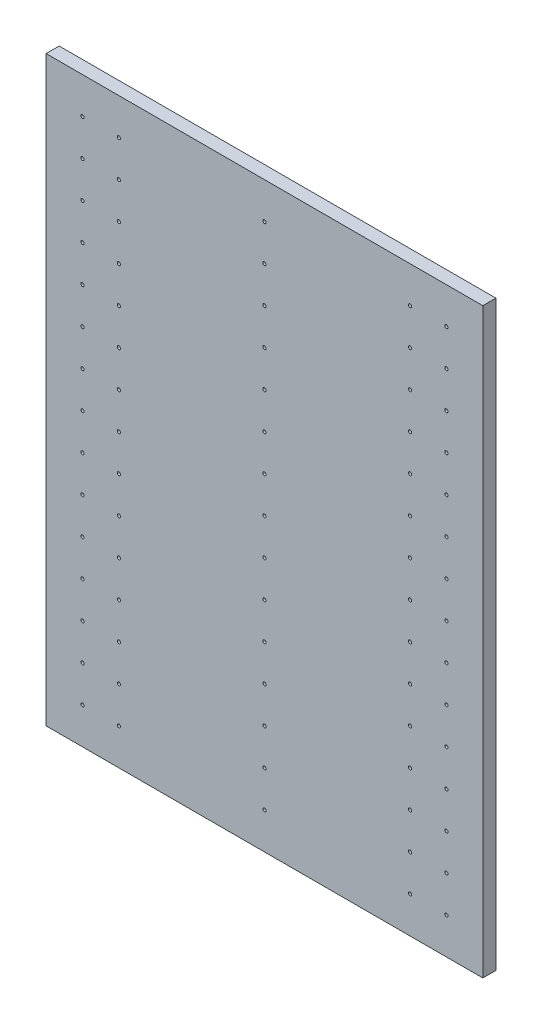
SolidWorks part; units mm, degrees
ref_plane "Спереди" through (0, 0, 0) normal (0, 0, 1) x (1, 0, 0)
ref_plane "Сверху" through (0, 0, 0) normal (0, 1, 0) x (1, 0, 0)
ref_plane "Справа" through (0, 0, 0) normal (1, 0, 0) x (0, 0, -1)
sketch "Эскиз1" plane through (0, 0, 0) normal (0, 0, 1) x (1, 0, 0)
  line L1 (0, 0) -> (600, 0)
  line L2 (0, 0) -> (0, 800)
  line L3 (0, 800) -> (600, 800)
  line L4 (600, 0) -> (600, 800)
extrude "Бобышка-Вытянуть1" add sketch "Эскиз1" along normal blind 18
sketch "Эскиз2" plane through (0, 0, 18) normal (0, 0, 1) x (1, 0, 0)
  circle A0 centre (550, 50) radius 2.25
  circle A1 centre (300, 50) radius 2.25
  circle A2 centre (500, 50) radius 2.25
  circle A3 centre (100, 50) radius 2.25
  circle A4 centre (50, 50) radius 2.25
  circle A60 centre (550, 100) radius 2.25
  circle A61 centre (300, 100) radius 2.25
  circle A62 centre (500, 100) radius 2.25
  circle A63 centre (100, 100) radius 2.25
  circle A64 centre (50, 100) radius 2.25
  circle A65 centre (550, 150) radius 2.25
  circle A66 centre (300, 150) radius 2.25
  circle A67 centre (500, 150) radius 2.25
  circle A68 centre (100, 150) radius 2.25
  circle A69 centre (50, 150) radius 2.25
  circle A70 centre (550, 200) radius 2.25
  circle A71 centre (300, 200) radius 2.25
  circle A72 centre (500, 200) radius 2.25
  circle A73 centre (100, 200) radius 2.25
  circle A74 centre (50, 200) radius 2.25
  circle A75 centre (550, 250) radius 2.25
  circle A76 centre (300, 250) radius 2.25
  circle A77 centre (500, 250) radius 2.25
  circle A78 centre (100, 250) radius 2.25
  circle A79 centre (50, 250) radius 2.25
  circle A80 centre (550, 300) radius 2.25
  circle A81 centre (300, 300) radius 2.25
  circle A82 centre (500, 300) radius 2.25
  circle A83 centre (100, 300) radius 2.25
  circle A84 centre (50, 300) radius 2.25
  circle A85 centre (550, 350) radius 2.25
  circle A86 centre (300, 350) radius 2.25
  circle A87 centre (500, 350) radius 2.25
  circle A88 centre (100, 350) radius 2.25
  circle A89 centre (50, 350) radius 2.25
  circle A90 centre (550, 400) radius 2.25
  circle A91 centre (300, 400) radius 2.25
  circle A92 centre (500, 400) radius 2.25
  circle A93 centre (100, 400) radius 2.25
  circle A94 centre (50, 400) radius 2.25
  circle A95 centre (550, 450) radius 2.25
  circle A96 centre (300, 450) radius 2.25
  circle A97 centre (500, 450) radius 2.25
  circle A98 centre (100, 450) radius 2.25
  circle A99 centre (50, 450) radius 2.25
  circle A100 centre (550, 500) radius 2.25
  circle A101 centre (300, 500) radius 2.25
  circle A102 centre (500, 500) radius 2.25
  circle A103 centre (100, 500) radius 2.25
  circle A104 centre (50, 500) radius 2.25
  circle A105 centre (550, 550) radius 2.25
  circle A106 centre (300, 550) radius 2.25
  circle A107 centre (500, 550) radius 2.25
  circle A108 centre (100, 550) radius 2.25
  circle A109 centre (50, 550) radius 2.25
  circle A110 centre (550, 600) radius 2.25
  circle A111 centre (300, 600) radius 2.25
  circle A112 centre (500, 600) radius 2.25
  circle A113 centre (100, 600) radius 2.25
  circle A114 centre (50, 600) radius 2.25
  circle A115 centre (550, 650) radius 2.25
  circle A116 centre (300, 650) radius 2.25
  circle A117 centre (500, 650) radius 2.25
  circle A118 centre (100, 650) radius 2.25
  circle A119 centre (50, 650) radius 2.25
  circle A120 centre (550, 700) radius 2.25
  circle A121 centre (300, 700) radius 2.25
  circle A122 centre (500, 700) radius 2.25
  circle A123 centre (100, 700) radius 2.25
  circle A124 centre (50, 700) radius 2.25
  circle A125 centre (550, 750) radius 2.25
  circle A126 centre (300, 750) radius 2.25
  circle A127 centre (500, 750) radius 2.25
  circle A128 centre (100, 750) radius 2.25
  circle A129 centre (50, 750) radius 2.25
  dimension "D1" = 15
extrude "Вырез-Вытянуть1" cut sketch "Эскиз2" against normal blind 9
